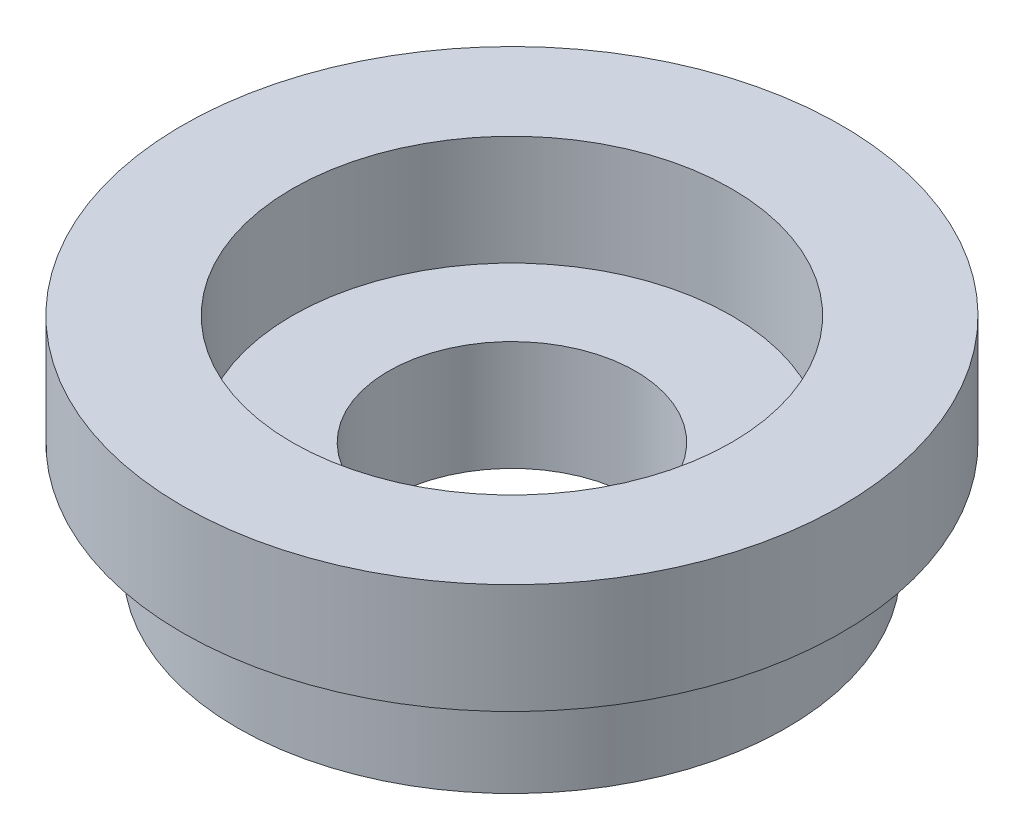
SolidWorks part; units mm, degrees
material "7075-T6 (SN)"
ref_plane "정면" through (0, 0, 0) normal (0, 0, 1) x (1, 0, 0)
ref_plane "윗면" through (0, 0, 0) normal (0, 1, 0) x (1, 0, 0)
ref_plane "우측면" through (0, 0, 0) normal (1, 0, 0) x (0, 0, -1)
sketch "스케치1" plane through (0, 0, 0) normal (0, 1, 0) x (1, 0, 0)
  circle A0 centre (0, 0) radius 5
  dimension "D1" = 10
extrude "보스-돌출1" add sketch "스케치1" along normal blind 2 contours A0
sketch "스케치2" plane through (0, 2, 0) normal (0, 1, 0) x (1, 0, 0)
  circle A0 centre (0, 0) radius 6
  dimension "D1" = 12
extrude "보스-돌출2" add sketch "스케치2" along normal blind 2
hole_wizard "M4 육각 소켓 머리 캡 나사용 카운터보어1" positions "스케치6" profile "스케치7" counterbore size "M4" standard "ISO" end condition through all
sketch "스케치6" plane through (0, 4, 0) normal (0, 1, 0) x (1, 0, 0)
  point P0 (0, 0)
sketch "스케치7" plane through (0, 4, 0) normal (1, 0, 0) x (0, 0, 1)
  line L0 (0, 0) -> (0, 4)
  line L1 (0, 4) -> (2.25, 4)
  line L3 (2.25, 4) -> (2.25, 2)
  line L4 (2.25, 2) -> (4, 2)
  line L5 (4, 2) -> (4, 0)
  line L7 (4, 0) -> (0, 0)
  line L11 (0, -6.35) -> (0, 107.95) construction
  dimension "관통 구멍 지름" = 4.5
  dimension "관통 구멍 깊이" = 4
  dimension "카운터보어 지름" = 8
  dimension "카운터보어 깊이" = 2
